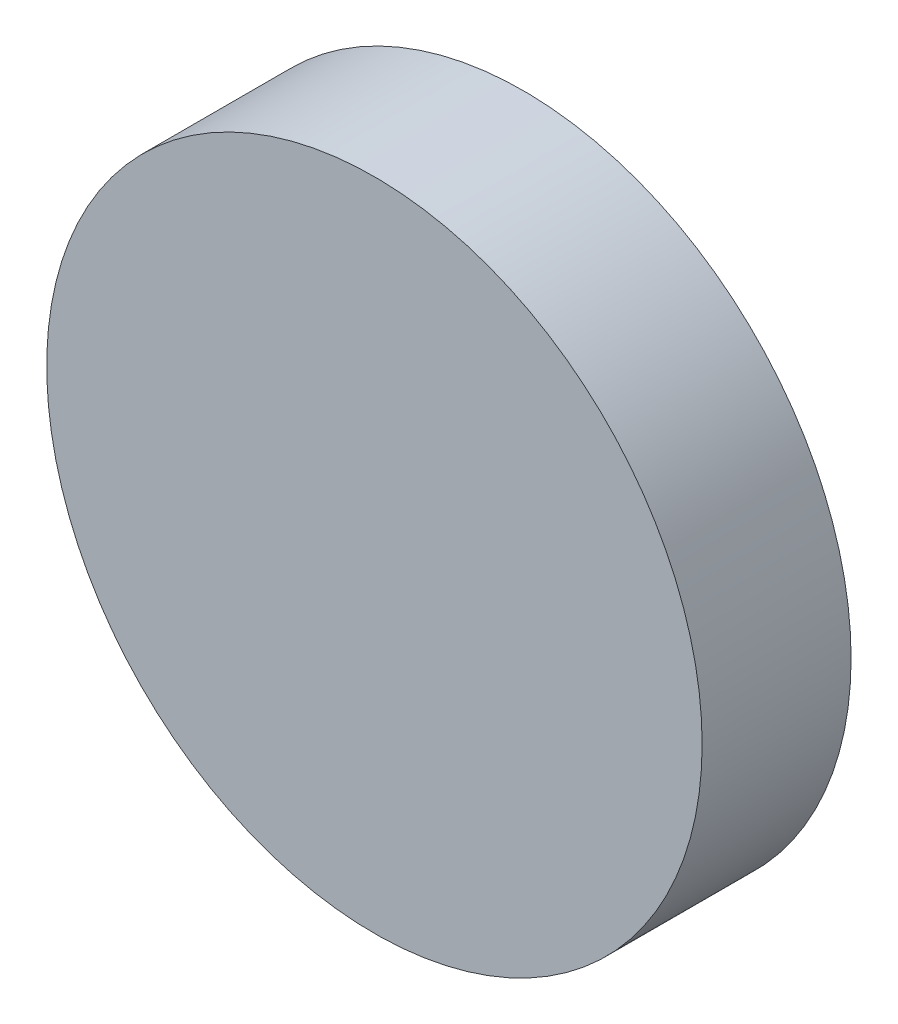
SolidWorks part; units mm, degrees
ref_plane "Front Plane" through (0, 0, 0) normal (0, 0, 1) x (1, 0, 0)
ref_plane "Top Plane" through (0, 0, 0) normal (0, 1, 0) x (1, 0, 0)
ref_plane "Right Plane" through (0, 0, 0) normal (1, 0, 0) x (0, 0, -1)
sketch "Sketch1" plane through (0, 0, 0) normal (0, 1, 0) x (1, 0, 0)
  line L0 (0, 0) -> (0, 26) construction
  line L1 (0, 0) -> (-22, 0)
  line L2 (-22, 0) -> (-22, 10)
  line L3 (0, 13) -> (0, 0)
  arc A0 (0, 13) -> (-22, 10) centre (-3.9692, -40.059) ccw
  dimension "D1" = 44
  dimension "D2" = 3
  dimension "D3" = 10
revolve "Revolve1" add sketch "Sketch1" angle 360 about L0
